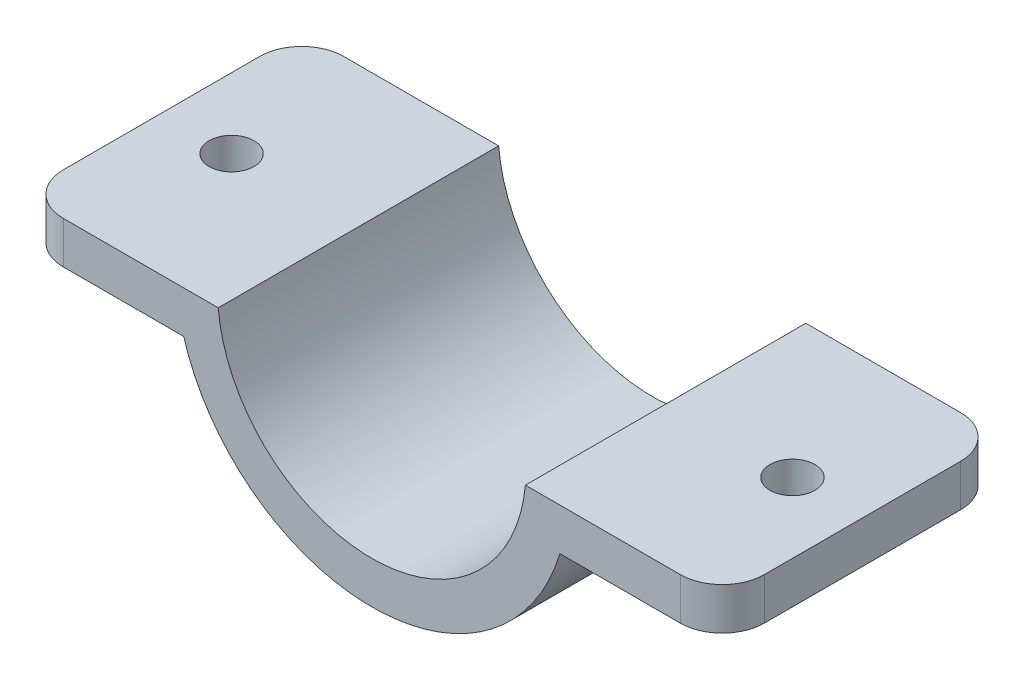
SolidWorks part; units mm, degrees
ref_plane "Front Plane" through (0, 0, 0) normal (0, 0, 1) x (1, 0, 0)
ref_plane "Top Plane" through (0, 0, 0) normal (0, 1, 0) x (1, 0, 0)
ref_plane "Right Plane" through (0, 0, 0) normal (1, 0, 0) x (0, 0, -1)
sketch "Sketch1" plane through (0, 0, 0) normal (0, 0, 1) x (1, 0, 0)
  line L0 (-25, -1) -> (25, -1)
  line L1 (25, -1) -> (25, -4)
  line L2 (25, -4) -> (13.4164, -4)
  line L3 (-25, -1) -> (-25, -4)
  line L4 (-25, -4) -> (-13.4164, -4)
  circle A0 centre (0, 0) radius 14
  circle A1 centre (0, 0) radius 11
  point P10 (0, -1)
  dimension "D2" = 22
  dimension "D3" = 3
  dimension "D1" = 50
  dimension "D4" = 3
  dimension "D5" = 1
extrude "Boss-Extrude1" add sketch "Sketch1" along normal blind 20 contours A1 L0 A0 | A0 L0 L3 L4 | A0 L2 L1 L0
sketch "Sketch2" plane through (0, -4, 0) normal (0, -1, 0) x (1, 0, 0)
  line L1 (-25, 20) -> (-25, 0) construction
  line L2 (-25, 20) -> (-25, 0) construction
  circle A0 centre (-20, 10) radius 1.6
  point P6 (-25, 10)
  dimension "D1" = 3.2
  dimension "D2" = 5
extrude "Cut-Extrude1" cut sketch "Sketch2" against normal blind 20
mirror "Mirror1" about plane through (0, 0, 0) normal (1, 0, 0) of "Cut-Extrude1"
fillet "Fillet1" radius 3 4 edges at (25, -2.5, 0) (25, -2.5, 20) (-25, -2.5, 0) (-25, -2.5, 20)
